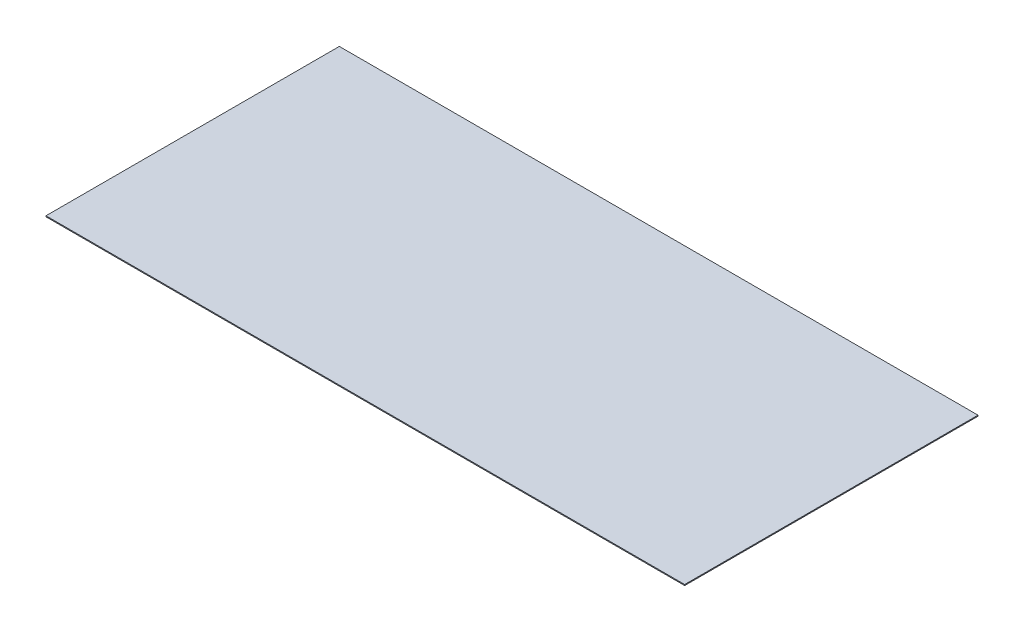
SolidWorks part; units mm, degrees
ref_plane "Front Plane" through (0, 0, 0) normal (0, 0, 1) x (1, 0, 0)
ref_plane "Top Plane" through (0, 0, 0) normal (0, 1, 0) x (1, 0, 0)
ref_plane "Right Plane" through (0, 0, 0) normal (1, 0, 0) x (0, 0, -1)
sketch "Sketch1" plane through (0, 0, 0) normal (0, 1, 0) x (1, 0, 0)
  line L1 (-337.5, 155) -> (337.5, 155)
  line L2 (-337.5, 155) -> (-337.5, -155)
  line L3 (-337.5, -155) -> (337.5, -155)
  line L4 (337.5, 155) -> (337.5, -155)
  line L5 (-337.5, 155) -> (337.5, -155) construction
  line L6 (-337.5, -155) -> (337.5, 155) construction
  point P0 (0, 0)
  dimension "D1" = 675
  dimension "D2" = 310
extrude "Boss-Extrude2" add sketch "Sketch1" along normal blind 1
